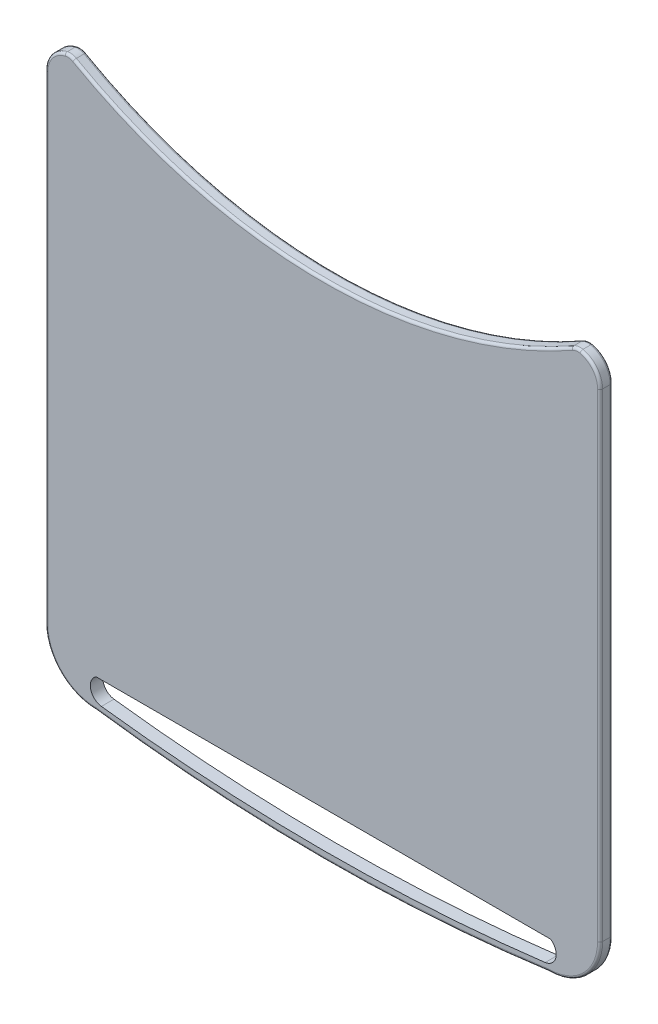
SolidWorks part; units mm, degrees
ref_plane "Front Plane" through (0, 0, 0) normal (0, 0, 1) x (1, 0, 0)
ref_plane "Top Plane" through (0, 0, 0) normal (0, 1, 0) x (1, 0, 0)
ref_plane "Right Plane" through (0, 0, 0) normal (1, 0, 0) x (0, 0, -1)
sketch "Sketch2" plane through (0, 0, 0) normal (0, 0, 1) x (1, 0, 0)
  line L2 (-71.6832, 36.2641) -> (-71.6832, -153.7359)
  line L4 (148.588, 36.2641) -> (148.588, -153.7359)
  line L16 (-51.5476, -162.2588) -> (128.989, -162.2588)
  arc A6 (128.4524, -173.8715) -> (148.588, -153.7359) centre (128.4524, -153.7359) ccw
  arc A7 (-71.6832, -153.7359) -> (-51.5476, -173.8715) centre (-51.5476, -153.7359) ccw
  arc A14 (148.588, 36.2641) -> (140.8078, 46.0146) centre (138.588, 36.2641) ccw
  arc A15 (-71.6832, 36.2641) -> (-63.9031, 46.0146) centre (-61.6832, 36.2641) cw
  arc A18 (-60.3287, 45.4898) -> (137.2335, 45.4898) centre (38.4524, 219.8689) ccw
  arc A19 (-51.5476, -173.8715) -> (128.4524, -173.8715) centre (38.4524, 485.6469) ccw
  arc A23 (-60.3287, 45.4898) -> (-63.9031, 46.0146) centre (-62.7932, 41.1393) ccw
  arc A24 (137.2335, 45.4898) -> (140.8078, 46.0146) centre (139.6979, 41.1393) cw
  arc A25 (-49.4217, -171.4022) -> (126.7823, -171.3455) centre (38.4524, 536.9799) ccw
  arc A26 (128.989, -162.2588) -> (126.7823, -171.3455) centre (126.1635, -166.384) cw
  arc A27 (-51.5476, -162.2588) -> (-49.4217, -171.4022) centre (-48.8062, -166.4403) ccw
extrude "Boss-Extrude1" add sketch "Sketch2" along normal blind 5
fillet "Fillet1" radius 1 22 edges at (-62.0668, 46.0863, 5) (138.9716, 46.0863, 5) (-62.0668, 46.0863, 0) (138.9716, 46.0863, 0) (-51.5476, -173.8715, 2.5) (38.4524, -179.9841, 5) (128.4524, -173.8715, 2.5) (38.4524, -179.9841, 0) (142.6904, -167.974, 0) (142.6904, -167.974, 5) (-65.7857, -167.974, 5) (-65.7857, -167.974, 0) (146.4046, 42.5011, 0) (146.4046, 42.5011, 5) (38.4524, 19.4549, 5) (-69.4998, 42.5011, 5) (-69.4998, 42.5011, 0) (-71.6832, -58.7359, 5) (-71.6832, -58.7359, 0) (38.4524, 19.4549, 0) (148.588, -58.7359, 5) (148.588, -58.7359, 0)
sketch "Sketch3" plane through (0, 0, 0) normal (0, 0, -1) x (-1, 0, 0)
  line L0 (-60.1934, -12.4411) -> (-80.1934, -23.9881)
  line L1 (-80.1934, -23.9881) -> (-80.1934, -47.0822)
  line L2 (-38.4524, -48.883) -> (-38.4524, -47.5162) construction
  line L3 (-54.316, -57.1088) -> (-53.7165, -57.6832) construction
  line L4 (-25.4081, -57.0793) -> (-24.9977, -56.651) construction
  line L6 (-39.2603, -48.4165) -> (-59.282, -59.976)
  line L7 (-59.282, -59.976) -> (-59.282, -83.095)
  line L8 (-59.282, -83.095) -> (-39.2603, -94.6545)
  line L9 (-39.2603, -94.6545) -> (-19.2387, -83.095)
  line L10 (-19.2387, -83.095) -> (-19.2387, -59.976)
  line L11 (-19.2387, -59.976) -> (-39.2603, -48.4165)
  line L23 (-59.6552, -84.6426) -> (-79.6552, -96.1896)
  line L24 (-79.6552, -96.1896) -> (-79.6552, -119.2836)
  line L25 (-79.6552, -119.2836) -> (-59.6552, -130.8306)
  line L26 (-59.6552, -130.8306) -> (-39.6552, -119.2836)
  line L27 (-39.6552, -119.2836) -> (-39.6552, -96.1896)
  line L28 (-39.6552, -96.1896) -> (-59.6552, -84.6426)
  line L29 (-18.4499, -84.1449) -> (-38.4499, -95.6919)
  line L30 (-38.4499, -95.6919) -> (-38.4499, -118.7859)
  line L31 (-38.4499, -118.7859) -> (-18.4499, -130.3329)
  line L32 (-18.4499, -130.3329) -> (1.5501, -118.7859)
  line L33 (1.5501, -118.7859) -> (1.5501, -95.6919)
  line L34 (1.5501, -95.6919) -> (-18.4499, -84.1449)
  line L41 (2.3037, -48.5964) -> (-17.6963, -60.1434)
  line L42 (-17.6963, -60.1434) -> (-17.6963, -83.2374)
  line L43 (-17.6963, -83.2374) -> (2.3037, -94.7844)
  line L44 (2.3037, -94.7844) -> (22.3037, -83.2374)
  line L45 (22.3037, -83.2374) -> (22.3037, -60.1434)
  line L46 (22.3037, -60.1434) -> (2.3037, -48.5964)
  line L47 (-80.1934, -47.0822) -> (-60.1934, -58.6292)
  line L48 (-60.1934, -58.6292) -> (-40.1934, -47.0822)
  line L49 (-40.1934, -47.0822) -> (-40.1934, -23.9881)
  line L50 (-40.1934, -23.9881) -> (-60.1934, -12.4411)
  line L51 (-80.4912, -48.7375) -> (-100.4912, -60.2845)
  line L52 (-100.4912, -60.2845) -> (-100.4912, -83.3785)
  line L53 (-100.4912, -83.3785) -> (-80.4912, -94.9255)
  line L54 (-80.4912, -94.9255) -> (-60.4912, -83.3785)
  line L55 (-60.4912, -83.3785) -> (-60.4912, -60.2845)
  line L56 (-60.4912, -60.2845) -> (-80.4912, -48.7375)
  line L63 (-18.7553, -12.5406) -> (-38.7553, -24.0876)
  line L64 (-38.7553, -24.0876) -> (-38.7553, -47.1816)
  line L65 (-38.7553, -47.1816) -> (-18.7553, -58.7286)
  line L66 (-18.7553, -58.7286) -> (1.2447, -47.1816)
  line L67 (1.2447, -47.1816) -> (1.2447, -24.0876)
  line L68 (1.2447, -24.0876) -> (-18.7553, -12.5406)
  circle A0 centre (-39.2603, -71.5355) radius 20.0216 construction
  point P4 (0, 0)
  point P9 (0, 0)
  point P26 (0, 0)
extrude "Boss-Extrude17" add sketch "Sketch3" along normal blind 7
chamfer "Chamfer1" distance 6 angle 45 6 edges at (60.4912, -71.8315, -7) (70.4912, -89.152, -7) (90.4912, -89.152, -7) (100.4912, -71.8315, -7) (90.4912, -54.511, -7) (70.4912, -54.511, -7)
chamfer "Chamfer2" distance 6 angle 45 6 edges at (-22.3037, -71.6904, -7) (-12.3037, -89.0109, -7) (7.6963, -89.0109, -7) (17.6963, -71.6904, -7) (7.6963, -54.3699, -7) (-12.3037, -54.3699, -7)
chamfer "Chamfer3" distance 6 angle 45 30 edges at (-1.5501, -107.2389, -7) (8.4499, -124.5594, -7) (28.4499, -124.5594, -7) (38.4499, -107.2389, -7) (28.4499, -89.9184, -7) (8.4499, -89.9184, -7) (-1.2447, -35.6346, -7) (8.7553, -52.9551, -7) (28.7553, -52.9551, -7) (38.7553, -35.6346, -7) (28.7553, -18.3141, -7) (8.7553, -18.3141, -7) (40.1934, -35.5351, -7) (50.1934, -52.8557, -7) (70.1934, -52.8557, -7) (80.1934, -35.5351, -7) (70.1934, -18.2146, -7) (50.1934, -18.2146, -7) (19.2387, -71.5355, -7) (29.2495, -88.8747, -7) (49.2712, -88.8747, -7) (59.282, -71.5355, -7) (49.2712, -54.1962, -7) (29.2495, -54.1962, -7) (39.6552, -107.7366, -7) (49.6552, -125.0571, -7) (69.6552, -125.0571, -7) (79.6552, -107.7366, -7) (69.6552, -90.4161, -7) (49.6552, -90.4161, -7)
